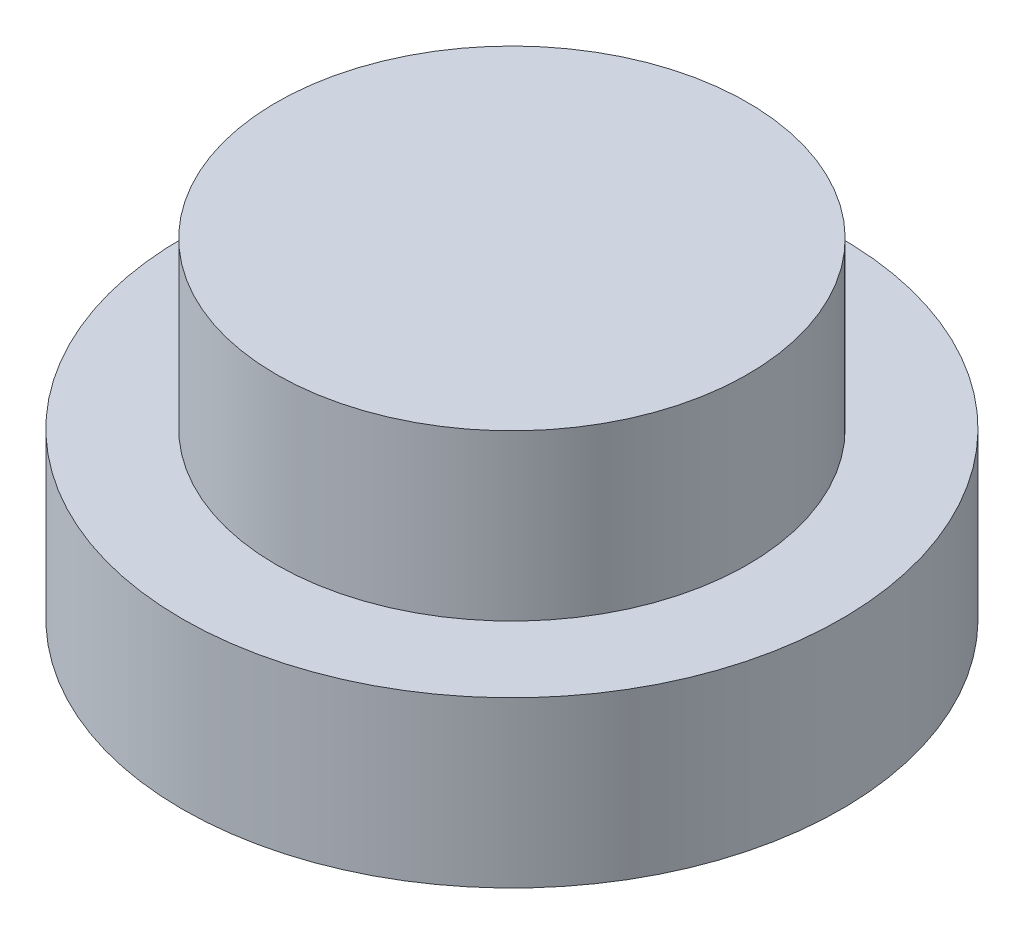
SolidWorks part; units mm, degrees
ref_plane "Front Plane" through (0, 0, 0) normal (0, 0, 1) x (1, 0, 0)
ref_plane "Top Plane" through (0, 0, 0) normal (0, 1, 0) x (1, 0, 0)
ref_plane "Right Plane" through (0, 0, 0) normal (1, 0, 0) x (0, 0, -1)
sketch "Sketch1" plane through (0, 0, 0) normal (0, 1, 0) x (1, 0, 0)
  circle A0 centre (0, 0) radius 2
extrude "Boss-Extrude1" add sketch "Sketch1" along normal blind 1
sketch "Sketch2" plane through (0, 1, 0) normal (0, 1, 0) x (1, 0, 0)
  circle A0 centre (0, 0) radius 1.43
extrude "Boss-Extrude2" add sketch "Sketch2" along normal blind 1
